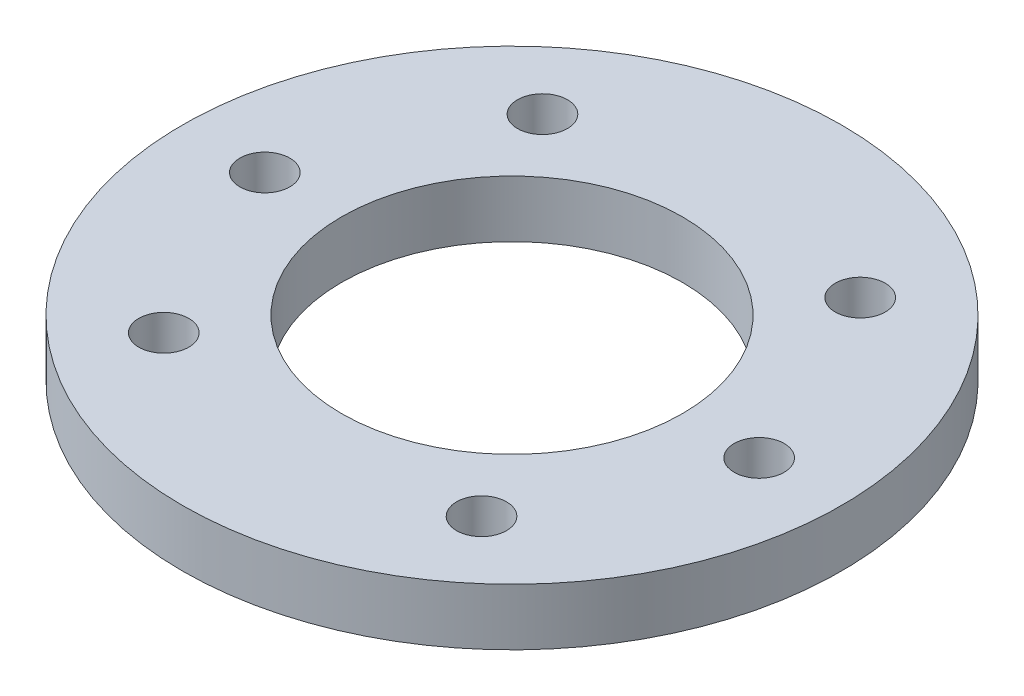
SolidWorks part; units mm, degrees
ref_plane "前视基准面" through (0, 0, 0) normal (0, 0, 1) x (1, 0, 0)
ref_plane "上视基准面" through (0, 0, 0) normal (0, 1, 0) x (1, 0, 0)
ref_plane "右视基准面" through (0, 0, 0) normal (1, 0, 0) x (0, 0, -1)
other "Configuration Table"
sketch "草图1" plane through (0, 0, 0) normal (0, 1, 0) x (1, 0, 0)
  line L0 (-13.9806, 16.6615) -> (0, 0) construction
  line L1 (0, -55) -> (0, 55) construction
  line L2 (13.9806, 16.6615) -> (0, 0) construction
  line L3 (-55, 0) -> (55, 0) construction
  circle A0 centre (0, 0) radius 29
  circle A1 centre (0, 0) radius 15
  circle A2 centre (0, 0) radius 21.75 construction
  circle A3 centre (-13.9806, 16.6615) radius 2.2
  circle A4 centre (13.9806, 16.6615) radius 2.2
  circle A5 centre (-21.75, 0) radius 2.2
  circle A6 centre (21.75, 0) radius 2.2
  circle A7 centre (13.9806, -16.6615) radius 2.2
  circle A8 centre (-13.9806, -16.6615) radius 2.2
  dimension "D1" = 58
  dimension "D2" = 30
  dimension "D3" = 43.5
  dimension "D4" = 80
  dimension "D5" = 4.4
extrude "凸台-拉伸1" add sketch "草图1" along normal blind 5
